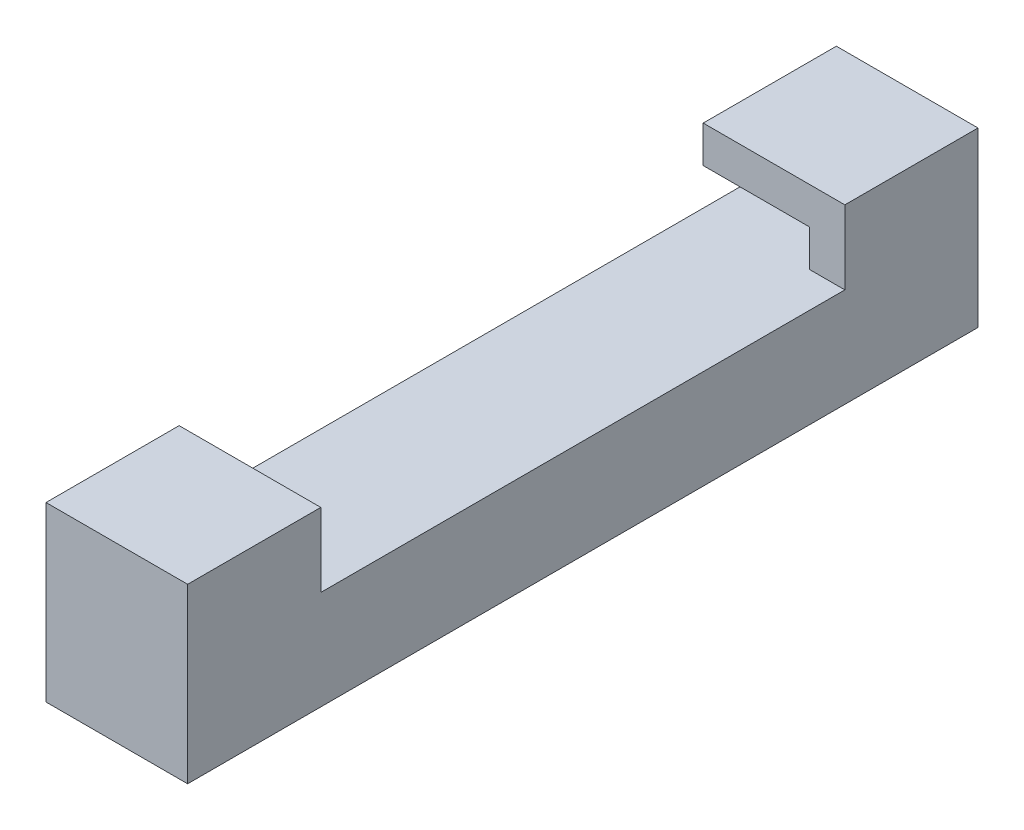
SolidWorks part; units mm, degrees
material "ABS"
ref_plane "Front Plane" through (0, 0, 0) normal (0, 0, 1) x (1, 0, 0)
ref_plane "Top Plane" through (0, 0, 0) normal (0, 1, 0) x (1, 0, 0)
ref_plane "Right Plane" through (0, 0, 0) normal (1, 0, 0) x (0, 0, -1)
sketch "Sketch1" plane through (0, 0, 0) normal (1, 0, 0) x (0, 0, -1)
  line L0 (0, 0) -> (80.01, 0)
  line L1 (80.01, 0) -> (80.01, 19.05)
  line L2 (80.01, 19.05) -> (71.12, 19.05)
  line L3 (71.12, 19.05) -> (71.12, 8.89)
  line L4 (71.12, 8.89) -> (8.89, 8.89)
  line L5 (8.89, 8.89) -> (8.89, 19.05)
  line L6 (8.89, 19.05) -> (0, 19.05)
  line L7 (0, 19.05) -> (0, 0)
  dimension "D1" = 62.23
  dimension "D2" = 8.89
  dimension "D3" = 8.89
  dimension "D4" = 8.89
  dimension "D5" = 10.16
  dimension "D6" = 10.16
extrude "Boss-Extrude1" add sketch "Sketch1" along normal blind 12.7
sketch "Sketch2" plane through (0, 0, 0) normal (-1, 0, 0) x (0, 0, 1)
  line L0 (-40.005, 8.89) -> (-63.5, 8.89) construction
  line L1 (-71.12, 8.89) -> (-8.89, 8.89) construction
  line L2 (-40.005, 8.89) -> (-16.51, 8.89) construction
  line L3 (-63.5, 8.89) -> (-63.5, 12.192) construction
  line L4 (-16.51, 8.89) -> (-16.51, 12.192) construction
  line L5 (-63.5, 12.192) -> (-70.612, 12.192)
  line L6 (-16.51, 12.192) -> (-9.398, 12.192)
  line L7 (-63.5, 12.192) -> (-63.5, 15.494)
  line L8 (-63.5, 15.494) -> (-74.93, 15.494)
  line L9 (-74.93, 15.494) -> (-74.93, 8.89)
  line L10 (-74.93, 8.89) -> (-70.612, 8.89)
  line L11 (-70.612, 8.89) -> (-70.612, 12.192)
  line L12 (-16.51, 12.192) -> (-16.51, 15.494)
  line L13 (-16.51, 15.494) -> (-5.08, 15.494)
  line L14 (-5.08, 15.494) -> (-5.08, 8.89)
  line L15 (-5.08, 8.89) -> (-9.398, 8.89)
  line L16 (-9.398, 8.89) -> (-9.398, 12.192)
  point P4 (0, 0)
  dimension "D1" = 23.495
  dimension "D2" = 23.495
  dimension "D3" = 3.302
  dimension "D4" = 3.302
  dimension "D5" = 7.112
  dimension "D6" = 7.112
  dimension "D7" = 3.302
  dimension "D8" = 11.43
  dimension "D9" = 11.43
extrude "Boss-Extrude3" add sketch "Sketch2" against normal blind 12.7
sketch "Sketch4" plane through (0, 0, 0) normal (-1, 0, 0) x (0, 0, 1)
  line L0 (-71.12, 15.494) -> (-75.438, 15.494)
  line L1 (-75.438, 15.494) -> (-75.438, 0)
  line L2 (0, 0) -> (-80.01, 0) construction
  line L3 (-75.438, 0) -> (-80.01, 0)
  line L4 (-80.01, 0) -> (-80.01, 19.05)
  line L5 (-80.01, 19.05) -> (-71.12, 19.05)
  line L6 (-71.12, 19.05) -> (-71.12, 15.494)
  dimension "D1" = 4.318
extrude "Cut-Extrude1" cut sketch "Sketch4" against normal up to next
sketch "Sketch5" plane through (0, 0, 0) normal (-1, 0, 0) x (0, 0, 1)
  line L0 (-8.89, 15.494) -> (-4.572, 15.494)
  line L1 (-4.572, 15.494) -> (-4.572, 0)
  line L2 (0, 0) -> (-75.438, 0) construction
  line L3 (-4.572, 0) -> (0, 0)
  line L4 (0, 0) -> (0, 19.05)
  line L5 (0, 19.05) -> (-8.89, 19.05)
  line L6 (-8.89, 19.05) -> (-8.89, 15.494)
  dimension "D1" = 4.318
extrude "Cut-Extrude2" cut sketch "Sketch5" against normal up to next
sketch "Sketch6" plane through (12.7, 0, 0) normal (1, 0, 0) x (0, 0, -1)
  line L0 (16.51, 12.192) -> (16.51, 8.89)
  line L1 (70.612, 8.89) -> (9.398, 8.89) construction
  line L2 (16.51, 8.89) -> (9.398, 8.89)
  line L3 (9.398, 8.89) -> (9.398, 12.192)
  line L4 (9.398, 12.192) -> (16.51, 12.192)
extrude "Boss-Extrude4" add sketch "Sketch6" against normal blind 3.175
sketch "Sketch7" plane through (12.7, 0, 0) normal (1, 0, 0) x (0, 0, -1)
  line L0 (63.5, 12.192) -> (63.5, 8.89)
  line L1 (70.612, 8.89) -> (16.51, 8.89) construction
  line L2 (63.5, 8.89) -> (70.612, 8.89)
  line L3 (70.612, 8.89) -> (70.612, 12.192)
  line L4 (70.612, 12.192) -> (63.5, 12.192)
extrude "Boss-Extrude5" add sketch "Sketch7" against normal blind 3.175
